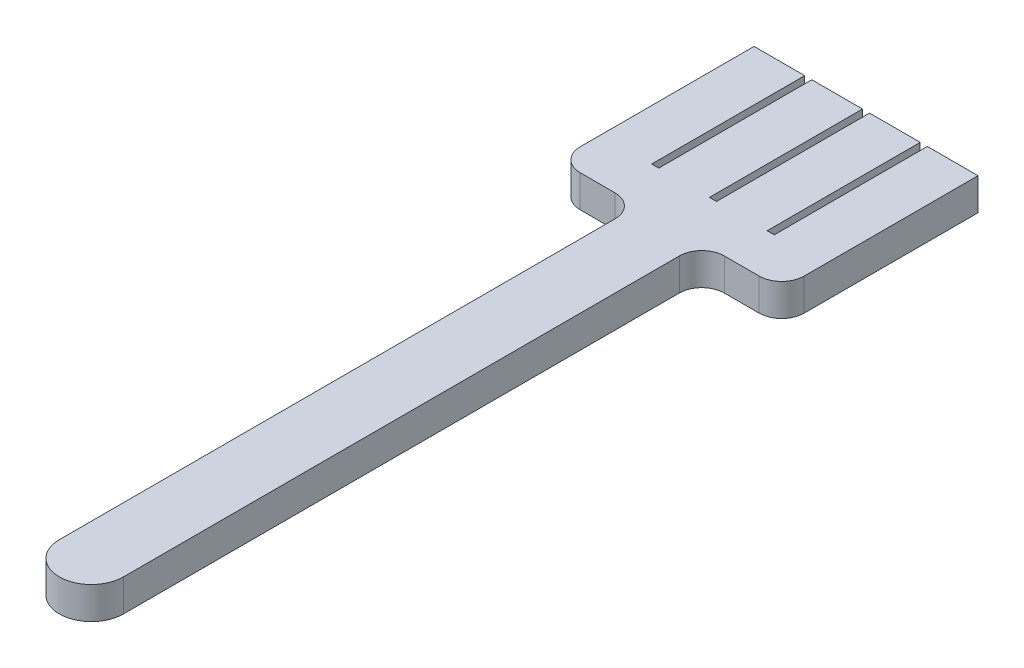
SolidWorks part; units mm, degrees
material "Pure Gold"
ref_plane "Front" through (0, 0, 0) normal (0, 0, 1) x (1, 0, 0)
ref_plane "Top" through (0, 0, 0) normal (0, 1, 0) x (1, 0, 0)
ref_plane "Right" through (0, 0, 0) normal (1, 0, 0) x (0, 0, -1)
sketch "Sketch1" plane through (0, 0, 0) normal (0, 1, 0) x (1, 0, 0)
  line L0 (0, 0) -> (0, 180)
  line L1 (0, 180) -> (-24.8495, 180)
  line L2 (-24.8495, 180) -> (-24.8495, 241.1057)
  line L3 (-24.8495, 241.1057) -> (-9.0817, 241.1057)
  line L4 (-9.0817, 241.1057) -> (-9.0817, 193.4694)
  line L5 (-9.0817, 193.4694) -> (-6.8724, 193.4694)
  line L6 (-6.8724, 193.4694) -> (-6.8724, 241.1057)
  line L7 (-6.8724, 241.1057) -> (8.8954, 241.1057)
  line L8 (8.8954, 241.1057) -> (8.8954, 193.4694)
  line L9 (8.8954, 193.4694) -> (11.1046, 193.4694)
  line L10 (11.1046, 193.4694) -> (11.1046, 241.1057)
  line L11 (11.1046, 241.1057) -> (26.8724, 241.1057)
  line L12 (26.8724, 241.1057) -> (26.8724, 193.4694)
  line L13 (26.8724, 193.4694) -> (29.0817, 193.4694)
  line L14 (29.0817, 193.4694) -> (29.0817, 241.1057)
  line L15 (29.0817, 241.1057) -> (44.8495, 241.1057)
  line L16 (44.8495, 241.1057) -> (44.8495, 180)
  line L17 (44.8495, 180) -> (20, 180)
  line L18 (20, 180) -> (20, 0)
  arc A0 (20, 0) -> (0, 0) centre (10, 0) cw
  dimension "D1" = 180
  dimension "D2" = 20
extrude "Boss-Extrude1" add sketch "Sketch1" along normal blind 10
fillet "Fillet2" radius 7 4 edges at (0, 5, -180) (20, 5, -180) (-24.8495, 5, -180) (44.8495, 5, -180)
